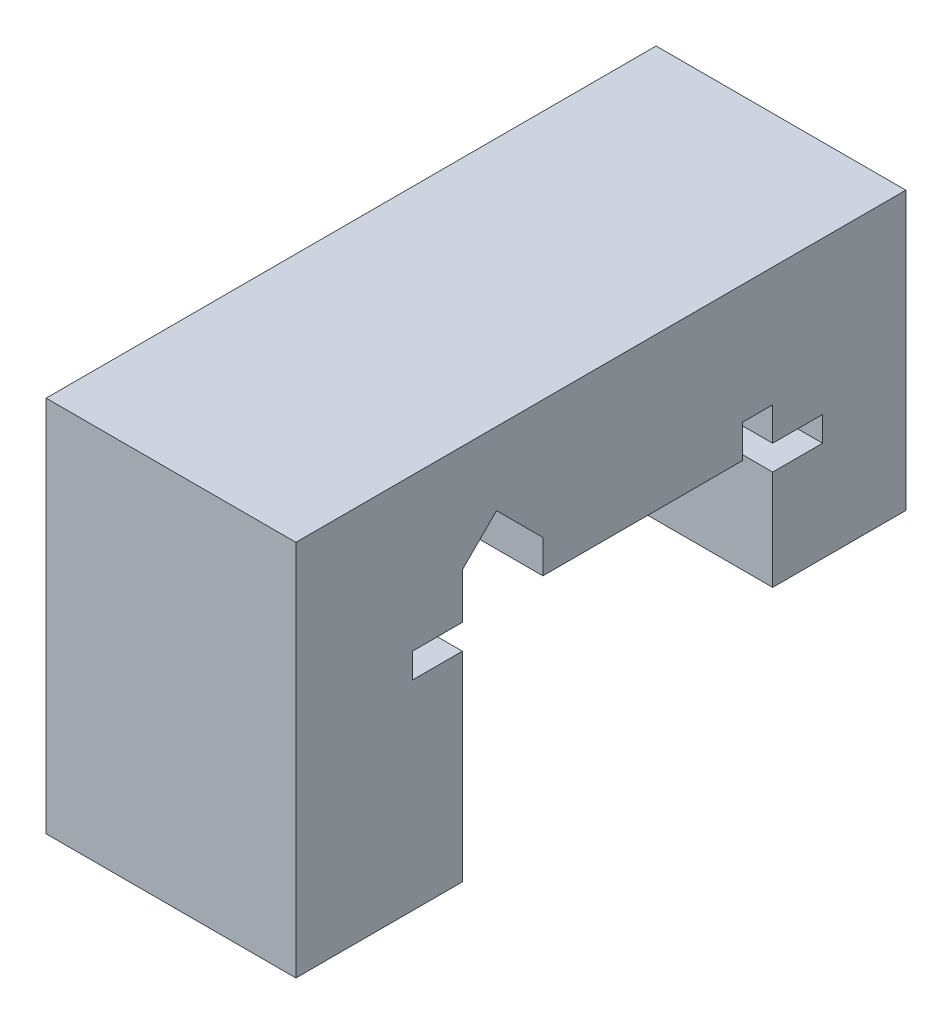
SolidWorks part; units mm, degrees
material "FG260"
ref_plane "Front Plane" through (0, 0, 0) normal (0, 0, 1) x (1, 0, 0)
ref_plane "Top Plane" through (0, 0, 0) normal (0, 1, 0) x (1, 0, 0)
ref_plane "Right Plane" through (0, 0, 0) normal (1, 0, 0) x (0, 0, -1)
sketch "Sketch2" plane through (0, 0, 0) normal (1, 0, 0) x (0, 0, -1)
  line L0 (0, 0) -> (60, 0)
  line L7 (158.0039, 91.6336) -> (-208.3661, 91.6336)
  line L8 (0, 0) -> (-60, 0)
  line L12 (-208.3661, 91.6336) -> (-208.3661, -135)
  line L15 (-60, 0) -> (-60, 20)
  line L16 (-60, 20) -> (-87.86, 47.86)
  line L17 (-87.86, 47.86) -> (-108.3661, 27.3539)
  line L18 (-108.3661, 27.3539) -> (-108.3661, 0)
  line L19 (-108.3661, 0) -> (-138.3661, 0)
  line L20 (-138.3661, 0) -> (-138.3661, -15)
  line L21 (-138.3661, -15) -> (-108.3661, -15)
  line L22 (-108.3661, -15) -> (-108.3661, -135)
  line L23 (-108.3661, -135) -> (-208.3661, -135)
  line L24 (78.0039, 0) -> (78.0039, 20)
  line L25 (78.0039, 20) -> (60, 20)
  line L26 (60, 20) -> (60, 0)
  line L27 (78.0039, 0) -> (108.0039, 0)
  line L28 (108.0039, 0) -> (108.0039, -15)
  line L29 (108.0039, -15) -> (78.0039, -15)
  line L30 (78.0039, -15) -> (78.0039, -75)
  line L31 (78.0039, -75) -> (158.0039, -75)
  line L32 (158.0039, -75) -> (158.0039, 91.6336)
  dimension "D1" = 60
  dimension "D2" = 45
  dimension "D3" = 39.4
  dimension "D4" = 29
  dimension "D5" = 30
  dimension "D6" = 30
  dimension "D7" = 15
  dimension "D8" = 30
  dimension "D9" = 120
  dimension "D10" = 60
  dimension "D11" = 18.0039
  dimension "D12" = 100
  dimension "D13" = 226.6336
  dimension "D14" = 20
  dimension "D15" = 20
  dimension "D16" = 15
  dimension "D17" = 30
  dimension "D18" = 60
  dimension "D19" = 80
extrude "Boss-Extrude1" add sketch "Sketch2" along normal blind 150
